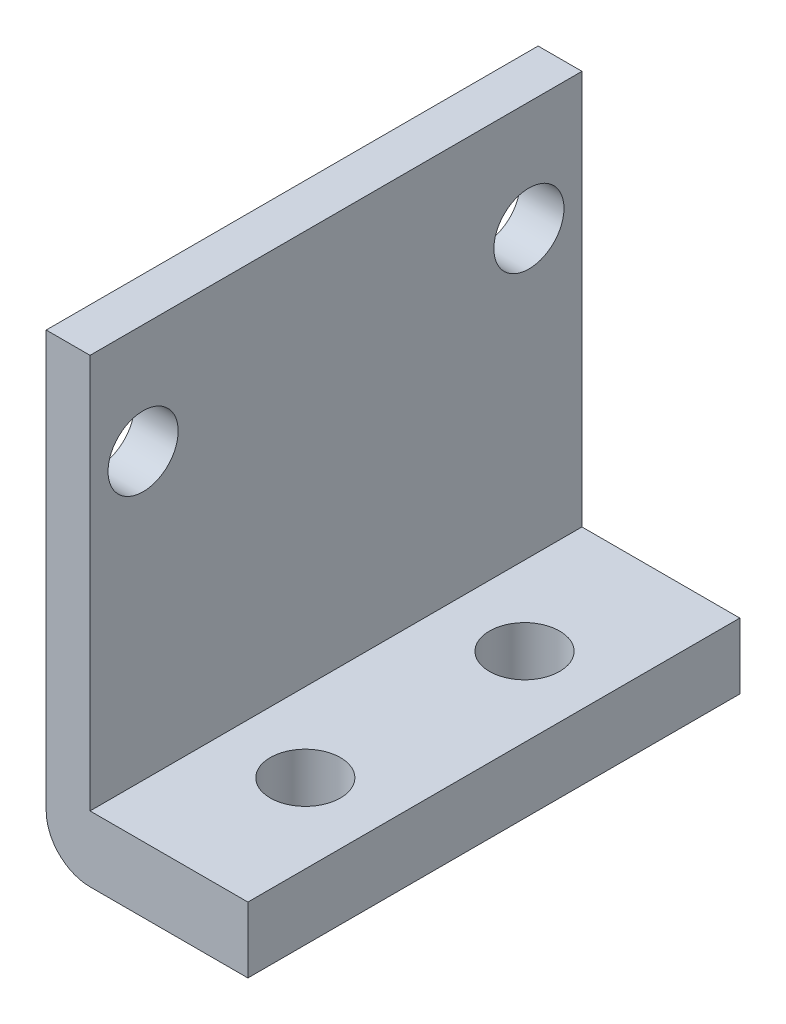
SolidWorks part; units mm, degrees
ref_plane "Front Plane" through (0, 0, 0) normal (0, 0, 1) x (1, 0, 0)
ref_plane "Top Plane" through (0, 0, 0) normal (0, 1, 0) x (1, 0, 0)
ref_plane "Right Plane" through (0, 0, 0) normal (1, 0, 0) x (0, 0, -1)
sketch "Sketch2" plane through (0, 0, 0) normal (0, 1, 0) x (1, 0, 0)
  line L0 (2, 22.44) -> (2, 0) construction
  line L1 (0, 0) -> (9.2, 0)
  line L2 (0, 0) -> (0, 22.44)
  line L3 (0, 22.44) -> (9.2, 22.44)
  line L4 (9.2, 0) -> (9.2, 22.44)
  line L5 (0, 11.22) -> (9.2, 11.22) construction
  line L6 (5.6, 11.22) -> (5.6, 16.22) construction
  line L7 (5.6, 11.22) -> (5.6, 6.22) construction
  circle A0 centre (5.6, 16.22) radius 1.6
  circle A1 centre (5.6, 6.22) radius 1.6
  dimension "D6" = 3.2
  dimension "D8" = 3.2
  dimension "D1" = 22.44
  dimension "D2" = 9.2
  dimension "D3" = 2
  dimension "D4" = 5
  dimension "D5" = 3.6
  dimension "D7" = 5
extrude "Boss-Extrude2" add sketch "Sketch2" along normal blind 3
sketch "Sketch4" plane through (0, 3, 0) normal (0, 1, 0) x (1, 0, 0)
  line L0 (0, 0) -> (9.2, 0) construction
  line L1 (0, 22.44) -> (2, 22.44)
  line L2 (0, 22.44) -> (0, 0)
  line L3 (0, 0) -> (2, 0)
  line L4 (2, 22.44) -> (2, 0)
  dimension "D1" = 2
extrude "Boss-Extrude3" add sketch "Sketch4" along normal blind 18 contours L2 L1 L4 L3
fillet "Fillet1" radius 2 1 edges at (0, 0, -11.22)
sketch "Sketch5" plane through (2, 0, 0) normal (1, 0, 0) x (0, 0, -1)
  line L0 (11.22, 21) -> (11.22, 3) construction
  line L1 (22.44, 21) -> (0, 21) construction
  line L2 (0, 3) -> (22.44, 3) construction
  line L3 (2.42, 16) -> (20.02, 16) construction
  circle A0 centre (2.42, 16) radius 1.6
  circle A1 centre (20.02, 16) radius 1.6
  point P8 (11.22, 16)
  dimension "D3" = 3.2
  dimension "D4" = 3.2
  dimension "D1" = 17.6
  dimension "D2" = 5
extrude "Cut-Extrude1" cut sketch "Sketch5" against normal blind 18
